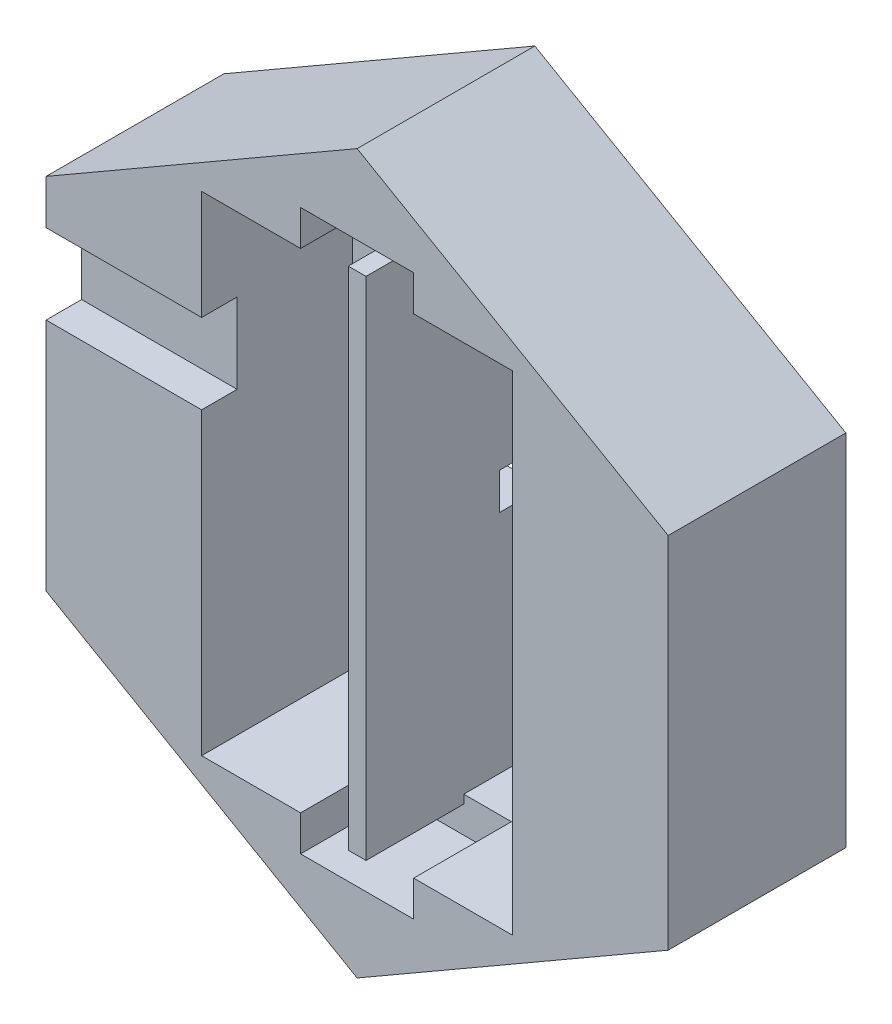
SolidWorks part; units mm, degrees
ref_plane "Front Plane" through (0, 0, 0) normal (0, 0, 1) x (1, 0, 0)
ref_plane "Top Plane" through (0, 0, 0) normal (0, 1, 0) x (1, 0, 0)
ref_plane "Right Plane" through (0, 0, 0) normal (1, 0, 0) x (0, 0, -1)
sketch "Sketch1" plane through (0, 0, 0) normal (0, 0, 1) x (1, 0, 0)
  line L1 (0, 404.1452) -> (-350, 202.0726)
  line L2 (-350, 202.0726) -> (-350, -202.0726)
  line L3 (-350, -202.0726) -> (0, -404.1452)
  line L4 (0, -404.1452) -> (350, -202.0726)
  line L5 (350, -202.0726) -> (350, 202.0726)
  line L6 (350, 202.0726) -> (0, 404.1452)
  circle A0 centre (0, 0) radius 350 construction
  dimension "D1" = 700
extrude "Boss-Extrude1" add sketch "Sketch1" along normal blind 200
sketch "Sketch2" plane through (0, 0, 200) normal (0, 0, 1) x (1, 0, 0)
  line L0 (0, 275) -> (0, -275) construction
  line L1 (-175, -275) -> (-10, -275)
  line L2 (-175, -275) -> (-175, 275)
  line L3 (-175, 275) -> (-10, 275)
  line L4 (175, -275) -> (175, 275)
  line L5 (-175, -275) -> (175, 275) construction
  line L6 (-175, 275) -> (175, -275) construction
  line L7 (-10, 275) -> (-10, -275)
  line L8 (10, 275) -> (10, -275)
  line L9 (10, 275) -> (175, 275)
  line L10 (10, -275) -> (175, -275)
  point P0 (0, 0)
  dimension "D1" = 550
  dimension "D2" = 350
  dimension "D3" = 10
  dimension "D4" = 10
extrude "Cut-Extrude1" cut sketch "Sketch2" against normal blind 170
sketch "Sketch4" plane through (0, 0, 0) normal (0, 0, -1) x (-1, 0, 0)
  line L0 (-350, 0) -> (350, 0) construction
  line L1 (-350, -202.0726) -> (-350, 202.0726) construction
  line L2 (350, 202.0726) -> (350, -202.0726) construction
  line L3 (-85, 20.5924) -> (85, 20.5924)
  line L4 (85, -20.5924) -> (-85, -20.5924)
  arc A0 (-85, 20.5924) -> (-85, -20.5924) centre (-85, 0) ccw
  arc A1 (85, -20.5924) -> (85, 20.5924) centre (85, 0) ccw
  dimension "D1" = 85
  dimension "D2" = 85
extrude "Cut-Extrude2" cut sketch "Sketch4" against normal blind 50
sketch "Sketch6" plane through (0, 0, 200) normal (0, 0, 1) x (1, 0, 0)
  line L0 (-10, 275) -> (-10, 284.635)
  line L1 (0, 0) -> (175, 0) construction
  line L2 (-63.6245, 275) -> (-63.6245, 315)
  line L3 (-63.6245, 315) -> (63.6245, 315)
  line L4 (63.6245, 275) -> (63.6245, 315)
  line L5 (175, -275) -> (175, 275) construction
  line L6 (55.5452, -275) -> (63.6245, -315) construction
  line L7 (-10, 284.635) -> (10, 284.635)
  line L8 (10, 284.635) -> (10, 275)
  line L9 (10, 275) -> (63.6245, 275)
  line L10 (175, 275) -> (10, 275) construction
  line L11 (-10, 275) -> (-63.6245, 275)
  line L12 (-10, 275) -> (-175, 275) construction
  line L13 (55.5452, 275) -> (63.6245, 315) construction
  line L14 (-10, -275) -> (-63.6245, -275)
  line L15 (10, -275) -> (63.6245, -275)
  line L16 (10, -284.635) -> (10, -275)
  line L17 (-10, -284.635) -> (10, -284.635)
  line L18 (63.6245, -275) -> (63.6245, -315)
  line L19 (-63.6245, -315) -> (63.6245, -315)
  line L20 (-63.6245, -275) -> (-63.6245, -315)
  line L21 (-10, -275) -> (-10, -284.635)
  point P0 (0, 0)
extrude "Cut-Extrude5" cut sketch "Sketch6" against normal blind 110
scale "Scale1" bodies to scale 106 scale about centroid uniform scaling yes scale factor 0.1
sketch "Sketch7" plane through (-35, 0, 0) normal (-1, 0, 0) x (0, 0, 1)
  line L0 (101.6433, 20.2073) -> (81.6433, 20.2073) construction
  line L1 (101.6504, 15.2073) -> (97.6504, 15.2073)
  line L2 (101.6504, 15.2073) -> (101.6504, 6.2073)
  line L3 (101.6504, 6.2073) -> (97.6504, 6.2073)
  line L4 (97.6504, 15.2073) -> (97.6504, 6.2073)
  point P5 (99.6504, 15.2073)
  dimension "D1" = 4
  dimension "D2" = 9
  dimension "D3" = 5
extrude "Cut-Extrude6" cut sketch "Sketch7" against normal up to surface (17.5 mm away) up to face at (-17.5, 0, 93.1433)
